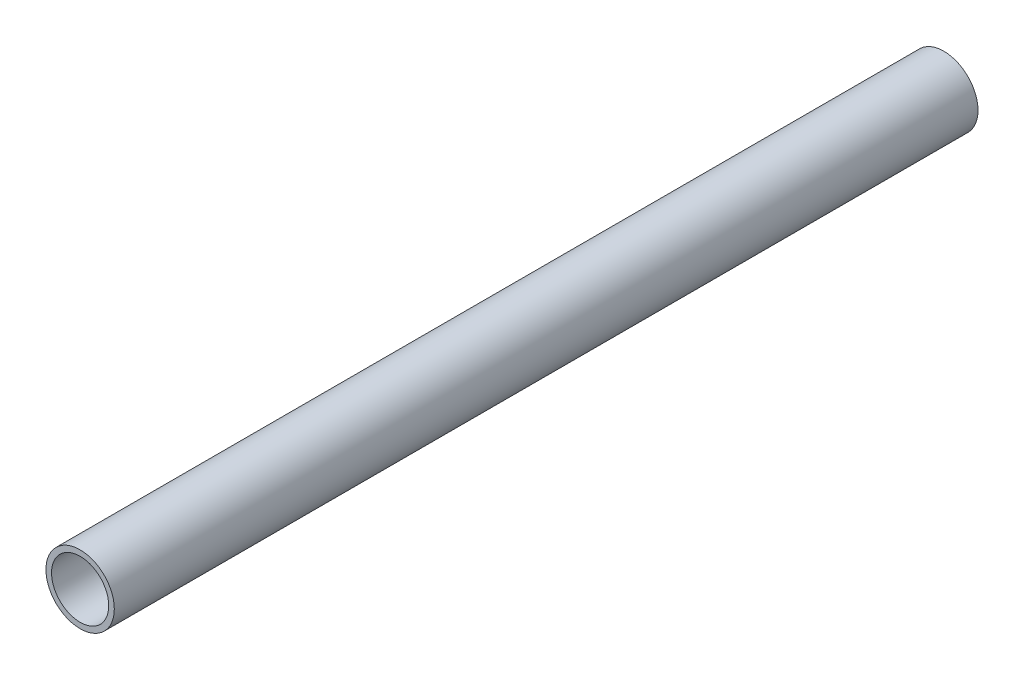
SolidWorks part; units mm, degrees
ref_plane "Front Plane" through (0, 0, 0) normal (0, 0, 1) x (1, 0, 0)
ref_plane "Top Plane" through (0, 0, 0) normal (0, 1, 0) x (1, 0, 0)
ref_plane "Right Plane" through (0, 0, 0) normal (1, 0, 0) x (0, 0, -1)
sketch "Sketch1" plane through (0, 0, 0) normal (0, 0, 1) x (1, 0, 0)
  circle A0 centre (0, 0) radius 24.13
  circle A1 centre (0, 0) radius 20.193
  dimension "D1" = 48.26
  dimension "D2" = 40.386
extrude "Boss-Extrude1" add sketch "Sketch1" along normal blind 609.6
